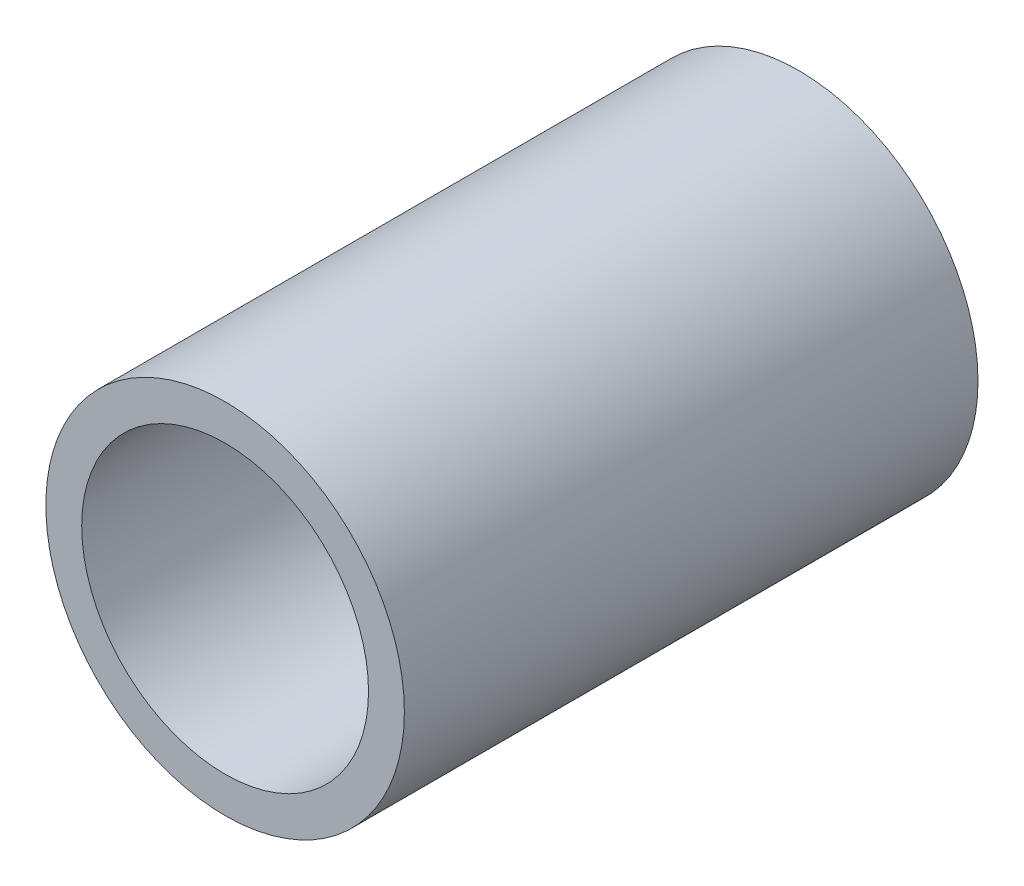
SolidWorks part; units mm, degrees
ref_plane "Front Plane" through (0, 0, 0) normal (0, 0, 1) x (1, 0, 0)
ref_plane "Top Plane" through (0, 0, 0) normal (0, 1, 0) x (1, 0, 0)
ref_plane "Right Plane" through (0, 0, 0) normal (1, 0, 0) x (0, 0, -1)
sketch "Sketch1" plane through (0, 0, 0) normal (0, 0, 1) x (1, 0, 0)
  circle A0 centre (0, 0) radius 5
  dimension "D1" = 10
extrude "Boss-Extrude1" add sketch "Sketch1" along normal blind 1
sketch "Sketch2" plane through (0, 0, 1) normal (0, 0, 1) x (1, 0, 0)
  circle A0 centre (0, 0) radius 5
  circle A1 centre (0, 0) radius 4
  dimension "D1" = 8
extrude "Boss-Extrude3" add sketch "Sketch2" along normal blind 15
